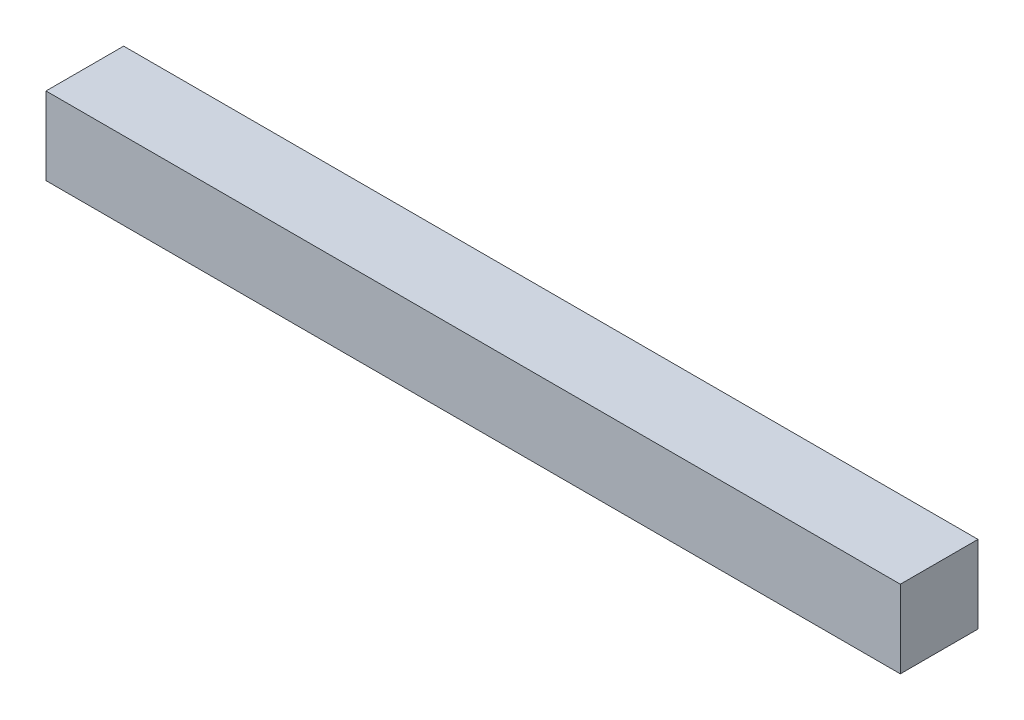
SolidWorks part; units mm, degrees
ref_plane "Front Plane" through (0, 0, 0) normal (0, 0, 1) x (1, 0, 0)
ref_plane "Top Plane" through (0, 0, 0) normal (0, 1, 0) x (1, 0, 0)
ref_plane "Right Plane" through (0, 0, 0) normal (1, 0, 0) x (0, 0, -1)
sketch "Sketch1" plane through (0, 0, 0) normal (1, 0, 0) x (0, 0, -1)
  line L1 (-15, -15) -> (15, -15)
  line L2 (-15, -15) -> (-15, 15)
  line L3 (-15, 15) -> (15, 15)
  line L4 (15, -15) -> (15, 15)
  line L5 (-15, -15) -> (15, 15) construction
  line L6 (-15, 15) -> (15, -15) construction
  point P0 (0, 0)
  dimension "D1" = 30
  dimension "D2" = 30
extrude "Boss-Extrude1" add sketch "Sketch1" along normal mid plane 330
